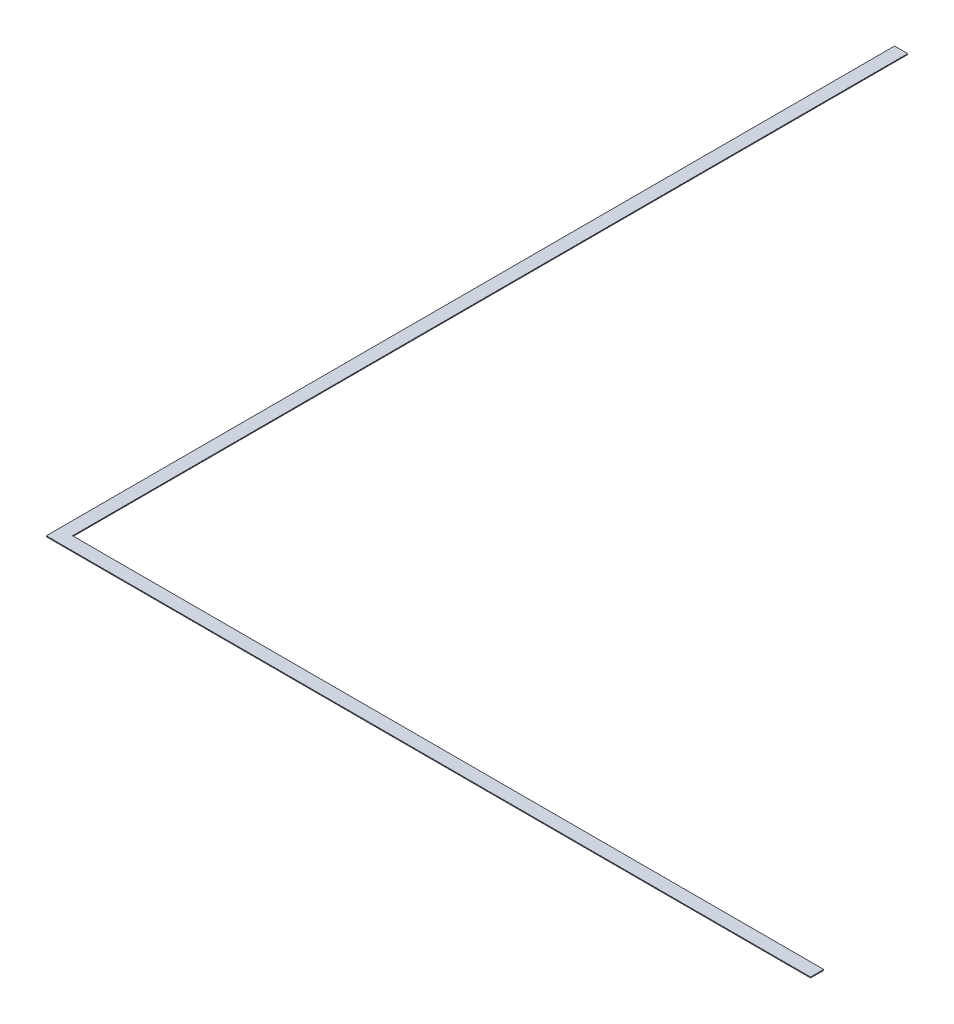
SolidWorks part; units mm, degrees
ref_plane "Front Plane" through (0, 0, 0) normal (0, 0, 1) x (1, 0, 0)
ref_plane "Top Plane" through (0, 0, 0) normal (0, 1, 0) x (1, 0, 0)
ref_plane "Right Plane" through (0, 0, 0) normal (1, 0, 0) x (0, 0, -1)
sketch "Sketch1" plane through (0, 0, 0) normal (0, 1, 0) x (1, 0, 0)
  line L1 (-1473.2, 1635.125) -> (1473.2, 1635.125)
  line L2 (-1473.2, 1635.125) -> (-1473.2, -1635.125)
  line L3 (-1473.2, -1635.125) -> (1473.2, -1635.125)
  line L4 (1473.2, 1635.125) -> (1473.2, -1635.125)
  line L5 (-1473.2, 1635.125) -> (1473.2, -1635.125) construction
  line L6 (-1473.2, -1635.125) -> (1473.2, 1635.125) construction
  line L7 (-1422.4, 1635.125) -> (1473.2, 1635.125)
  line L8 (-1422.4, 1635.125) -> (-1422.4, -1584.325)
  line L9 (-1422.4, -1584.325) -> (1473.2, -1584.325)
  line L10 (1473.2, 1635.125) -> (1473.2, -1584.325)
  point P0 (0, 0)
  dimension "D1" = 50.8
  dimension "D2" = 50.8
  dimension "D3" = 3270.25
  dimension "D4" = 2946.4
extrude "Boss-Extrude1" add sketch "Sketch1" along normal blind 3.175 contours L9 L8 L1 L2 L3 L4
